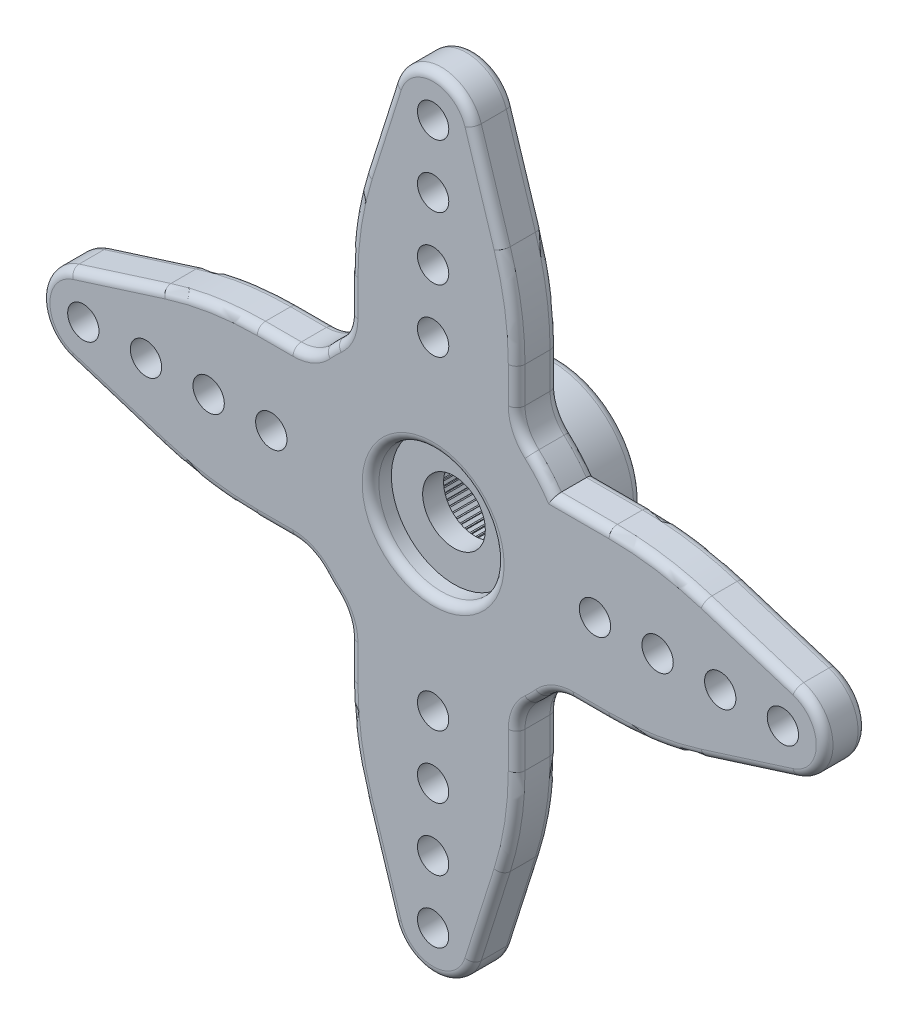
SolidWorks part; units mm, degrees
ref_plane "Ön Düzlem" through (0, 0, 0) normal (0, 0, 1) x (1, 0, 0)
ref_plane "Üst Düzlem" through (0, 0, 0) normal (0, 1, 0) x (1, 0, 0)
ref_plane "Sağ Düzlem" through (0, 0, 0) normal (1, 0, 0) x (0, 0, -1)
sketch "Sketch1" plane through (0, 0, 0) normal (0, 0, 1) x (1, 0, 0)
  line L0 (-4, 10.7446) -> (-4, 5.7446)
  line L1 (4, 10.7446) -> (4, 5.7446)
  line L2 (0, 0) -> (0, 16.75) construction
  line L3 (-4, 5.7446) -> (4, 5.7446) construction
  line L4 (-1.9067, 17.3539) -> (-4, 10.7446)
  line L5 (1.9067, 17.3539) -> (4, 10.7446)
  circle A0 centre (0, 0) radius 7
  circle A1 centre (0, 0) radius 18.75
  circle A2 centre (0, 16.75) radius 2
  circle A3 centre (0, 0) radius 1.5
  dimension "D1" = 37.5
  dimension "D2" = 14
  dimension "D3" = 4
  dimension "D5" = 3
  dimension "D4" = 5
  dimension "D6" = 8
extrude "Boss-Extrude1" add sketch "Sketch1" along normal blind 2 contours A0 A3 | A2 L4 L0 A0 L1 L5 | A2
fillet "Fillet1" radius 15 2 edges at (-4, 10.7446, 1) (4, 10.7446, 1)
sketch "Sketch2" plane through (0, 0, 2) normal (0, 0, 1) x (1, 0, 0)
  line L0 (0, 0) -> (0, 18.75) construction
  arc A0 (1.9067, 17.3539) -> (-1.9067, 17.3539) centre (0, 16.75) ccw construction
  circle A1 centre (0, 16.75) radius 0.75
  circle A2 centre (0, 13.75) radius 0.75
  circle A3 centre (0, 10.75) radius 0.75
  circle A4 centre (0, 7.75) radius 0.75
  dimension "D1" = 1.5
  dimension "D2" = 2
  dimension "D3" = 4
extrude "Cut-Extrude1" cut sketch "Sketch2" against normal through all
pattern_circular "CirPattern2" count 4 over 360 about axis through (0, 0, 0) along (0, 0, 1) of "Boss-Extrude1", "Fillet1", "Cut-Extrude1"
fillet "Fillet2" radius 2 7 edges at (4, 5.7446, 1) (-4, 5.7446, 1) (5.7446, -4, 1) (4, -5.7446, 1) (-5.7446, 4, 1) (-4, -5.7446, 1) (-5.7446, -4, 1)
sketch "Sketch3" plane through (0, 0, 2) normal (0, 0, 1) x (1, 0, 0)
  circle A0 centre (0, 0) radius 3
  dimension "D1" = 6
extrude "Cut-Extrude2" cut sketch "Sketch3" against normal blind 1
sketch "Sketch4" plane through (0, 0, 0) normal (0, 0, -1) x (-1, 0, 0)
  circle A0 centre (0, 0) radius 4
  circle A1 centre (0, 0) radius 3
  dimension "D1" = 8
  dimension "D2" = 6
extrude "Boss-Extrude2" add sketch "Sketch4" along normal blind 4
sketch "Sketch5" plane through (0, 0, -4) normal (0, 0, -1) x (-1, 0, 0)
  line L0 (0, 0) -> (0, -4) construction
  line L2 (0.025, -2.8941) -> (-0.025, -2.8941)
  line L3 (0.025, -2.8941) -> (0.025, -3.3941)
  line L4 (0.025, -3.3941) -> (-0.025, -3.3941)
  line L5 (-0.025, -2.8941) -> (-0.025, -3.3941)
  line L6 (0.025, -2.8941) -> (-0.025, -3.3941) construction
  line L7 (0.025, -3.3941) -> (-0.025, -2.8941) construction
  circle A1 centre (0, 0) radius 4 construction
  point P0 (0, -3.1441)
  dimension "D1" = 0.05
  dimension "D2" = 0.5
extrude "Boss-Extrude3" add sketch "Sketch5" against normal up to surface (4 mm away) up to face at (-3, 0, 0)
pattern_circular "CirPattern3" count 80 over 360 about axis through (0, 0, 0) along (0, 0, 1) of "Boss-Extrude3"
fillet "Fillet3" radius 0.4 81 edges at (-7.567, -4, 0) (-7.567, -4, 2) (-7.567, 4, 0) (-10.7173, 3.8239, 0) (-10.7173, -3.8239, 0) (-7.567, 4, 2) (-10.7173, 3.8239, 2) (-10.7173, -3.8239, 2) (4, -7.567, 0) (4, -7.567, 2) (-4, -7.567, 0) (-3.8239, -10.7173, 0) (3.8239, -10.7173, 0) (-4, -7.567, 2) (-3.8239, -10.7173, 2) (3.8239, -10.7173, 2) (7.0852, 4, 0) (7.0852, 4, 2) (7.567, -4, 0) (10.7173, -3.8239, 0) (10.7173, 3.8239, 0) (7.567, -4, 2) (10.7173, -3.8239, 2) (10.7173, 3.8239, 2) (2.6033, 15.1545, 2) (0, 18.75, 2) (4.9497, -4.9497, 0) (4.9497, -4.9497, 2) (-4.9497, 4.9497, 0) (-4.9497, 4.9497, 2) (-4.9497, -4.9497, 0) (-4.9497, -4.9497, 2) (-4, 7.567, 0) (-4, 7.567, 2) (5.8917, -4.1743, 0) (5.8917, -4.1743, 2) (4.1743, -5.8917, 0) (4.1743, -5.8917, 2) (-5.8917, 4.1743, 0) (-5.8917, 4.1743, 2) (-4.1743, -5.8917, 0) (-4.1743, -5.8917, 2) (-5.8917, -4.1743, 0) (-5.8917, -4.1743, 2) (4.1743, 5.8917, 0) (4.1743, 5.8917, 2) (-4.1743, 5.8917, 0) (-4.1743, 5.8917, 2) (-2.6033, 15.1545, 2) (4, 7.567, 0) (3.8239, 10.7173, 0) (-3.8239, 10.7173, 0) (3, 0, 2) (4, 7.567, 2) (4, 0, 0) (3.8239, 10.7173, 2) (-4, 0, -4) (-3.8239, 10.7173, 2) (5.2411, 4.6402, 0) (5.2411, 4.6402, 2) (-18.75, 0, 2) (-15.1545, -2.6033, 2) (0, -18.75, 2) (2.6033, -15.1545, 2) (18.75, 0, 2) (15.1545, 2.6033, 2) (-15.1545, 2.6033, 0) (-2.6033, -15.1545, 0) (15.1545, -2.6033, 0) (-15.1545, 2.6033, 2) (-18.75, 0, 0) (-15.1545, -2.6033, 0) (18.75, 0, 0) (15.1545, -2.6033, 2) (15.1545, 2.6033, 0) (-2.6033, -15.1545, 2) (0, -18.75, 0) (2.6033, -15.1545, 0) (-2.6033, 15.1545, 0) (0, 18.75, 0) (2.6033, 15.1545, 0)
